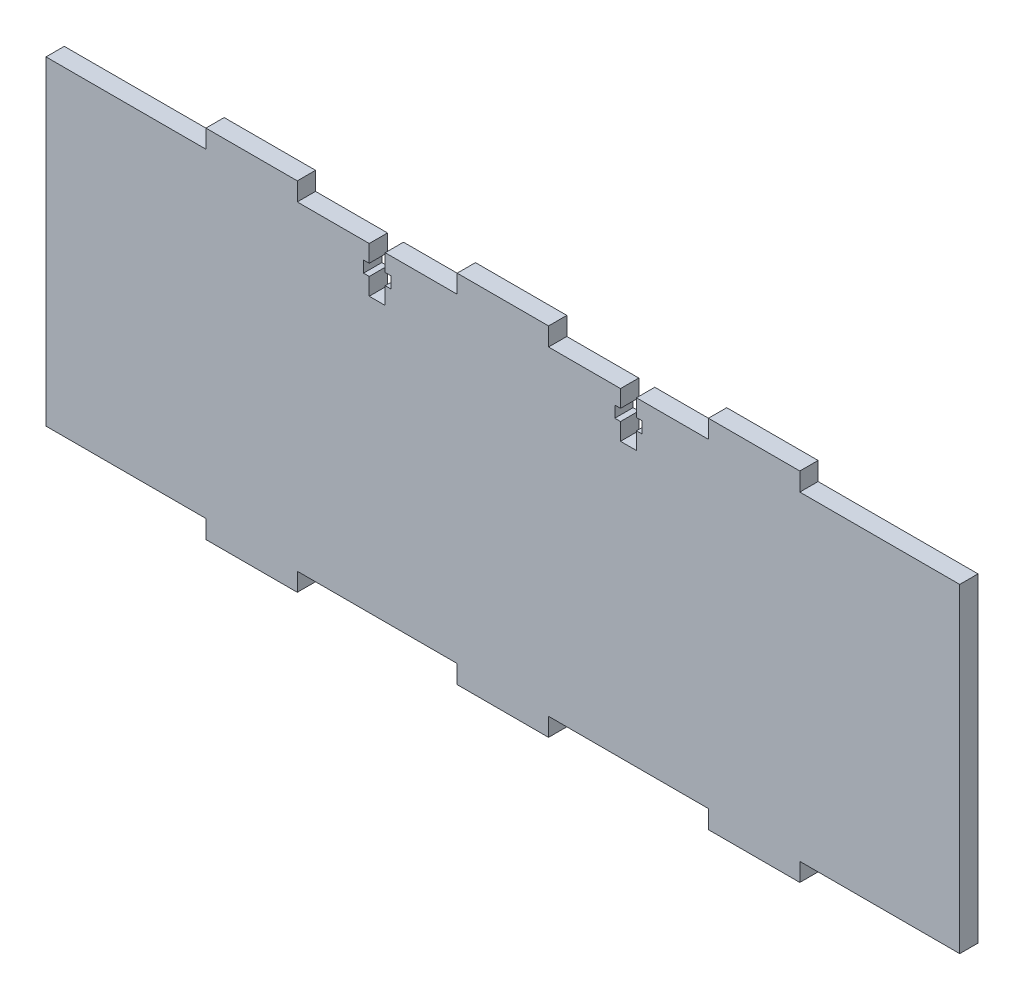
SolidWorks part; units mm, degrees
ref_plane "Front Plane" through (0, 0, 0) normal (0, 0, 1) x (1, 0, 0)
ref_plane "Top Plane" through (0, 0, 0) normal (0, 1, 0) x (1, 0, 0)
ref_plane "Right Plane" through (0, 0, 0) normal (1, 0, 0) x (0, 0, -1)
sketch "Sketch1" plane through (0, 0, 0) normal (0, 0, 1) x (1, 0, 0)
  line L1 (0, 0) -> (-200, 0)
  line L2 (0, 0) -> (0, 78)
  line L3 (0, 78) -> (-200, 78)
  line L4 (-200, 0) -> (-200, 78)
  dimension "D1" = 200
  dimension "D2" = 78
extrude "Boss-Extrude1" add sketch "Sketch1" along normal blind 4
sketch "Sketch2" plane through (0, 0, 4) normal (0, 0, 1) x (1, 0, 0)
  line L0 (-200, 74) -> (-200, 78)
  line L1 (-200, 78) -> (-200, 0) construction
  line L2 (-165, 74) -> (-145, 74)
  line L3 (0, 0) -> (0, 78) construction
  line L4 (0, 74) -> (0, 78)
  line L5 (0, 78) -> (-200, 78)
  line L6 (-165, 74) -> (-145, 74)
  line L7 (-110, 74) -> (-90, 74)
  line L8 (-55, 74) -> (-35, 74)
  line L9 (-110, 74) -> (-90, 74)
  line L10 (-55, 74) -> (-35, 74)
  line L11 (-200, 74) -> (-165, 74)
  line L12 (-145, 74) -> (-110, 74)
  line L13 (-90, 74) -> (-55, 74)
  line L14 (-35, 74) -> (0, 74)
  line L15 (-165, 74) -> (-165, 78)
  line L16 (-145, 74) -> (-145, 78)
  line L17 (-110, 74) -> (-110, 78)
  line L18 (-90, 74) -> (-90, 78)
  line L19 (-55, 74) -> (-55, 78)
  line L20 (-35, 74) -> (-35, 78)
  line L21 (-200, 39) -> (0, 39) construction
  line L22 (-35, 4) -> (-35, 0)
  line L23 (-55, 4) -> (-55, 0)
  line L24 (-90, 4) -> (-90, 0)
  line L25 (-110, 4) -> (-110, 0)
  line L26 (-145, 4) -> (-145, 0)
  line L27 (-165, 4) -> (-165, 0)
  line L28 (-35, 4) -> (0, 4)
  line L29 (-90, 4) -> (-55, 4)
  line L30 (-145, 4) -> (-110, 4)
  line L31 (-200, 4) -> (-165, 4)
  line L32 (-55, 4) -> (-35, 4)
  line L33 (-110, 4) -> (-90, 4)
  line L34 (-55, 4) -> (-35, 4)
  line L35 (-110, 4) -> (-90, 4)
  line L36 (-165, 4) -> (-145, 4)
  line L37 (0, 0) -> (-200, 0)
  line L38 (0, 4) -> (0, 0)
  line L39 (-165, 4) -> (-145, 4)
  line L40 (-200, 4) -> (-200, 0)
  line M9 (0, 0) -> (0, 78)
  line M10 (0, 78) -> (-200, 78)
  line M11 (-200, 78) -> (-200, 0)
  line M12 (-200, 0) -> (0, 0)
  dimension "D1" = 20
  dimension "D2" = 20
  dimension "D3" = 20
extrude "Cut-Extrude1" cut sketch "Sketch2" against normal up to surface (4 mm away) contours L11 L15 L5 M11 | L12 L17 L5 L16 | L13 L19 L5 L18 | L20 L14 M9 M10 | L31 L27 M11 M12 | L30 L26 L25 M12 | L29 L24 L23 M12 | L28 L22 M12 M9 up to face at (-100, 39, 0)
sketch "Sketch4" plane through (0, 0, 4) normal (0, 0, 1) x (1, 0, 0)
  line L0 (-127.5, 74) -> (-127.5, 64) construction
  line L1 (-124.5, 67.75) -> (-130.5, 70.25) construction
  line L2 (-124.5, 70.25) -> (-130.5, 67.75) construction
  line L3 (-127.5, 74) -> (-129.25, 74)
  line L4 (-100, 78) -> (-100, 0) construction
  line L13 (-127.5, 74) -> (-125.75, 74)
  line L14 (-129.25, 74) -> (-125.75, 74)
  line L15 (-90, 78) -> (-110, 78) construction
  line L16 (-110, 0) -> (-90, 0) construction
  line L17 (-75.5, 70.25) -> (-69.5, 67.75) construction
  line L18 (-75.5, 67.75) -> (-69.5, 70.25) construction
  line L19 (-72.5, 74) -> (-72.5, 64) construction
  line L20 (-69.5, 67.75) -> (-69.5, 70.25)
  line L21 (-75.5, 70.25) -> (-69.5, 70.25)
  line L22 (-75.5, 67.75) -> (-75.5, 70.25)
  line L23 (-75.5, 67.75) -> (-69.5, 67.75)
  line L24 (-74.25, 74) -> (-74.25, 64)
  line L25 (-70.75, 64) -> (-74.25, 64)
  line L26 (-70.75, 74) -> (-70.75, 64)
  line L27 (-70.75, 74) -> (-74.25, 74)
  line L28 (-72.5, 74) -> (-74.25, 74)
  line L29 (-72.5, 74) -> (-70.75, 74)
  line L30 (-129.25, 74) -> (-129.25, 64)
  line L31 (-129.25, 64) -> (-125.75, 64)
  line L32 (-125.75, 74) -> (-125.75, 64)
  line L33 (-124.5, 67.75) -> (-130.5, 67.75)
  line L34 (-124.5, 67.75) -> (-124.5, 70.25)
  line L35 (-124.5, 70.25) -> (-130.5, 70.25)
  line L36 (-130.5, 67.75) -> (-130.5, 70.25)
  point P10 (-127.5, 69)
  point P29 (-72.5, 69)
extrude "Cut-Extrude2" cut sketch "Sketch4" against normal up to surface (4 mm away)
